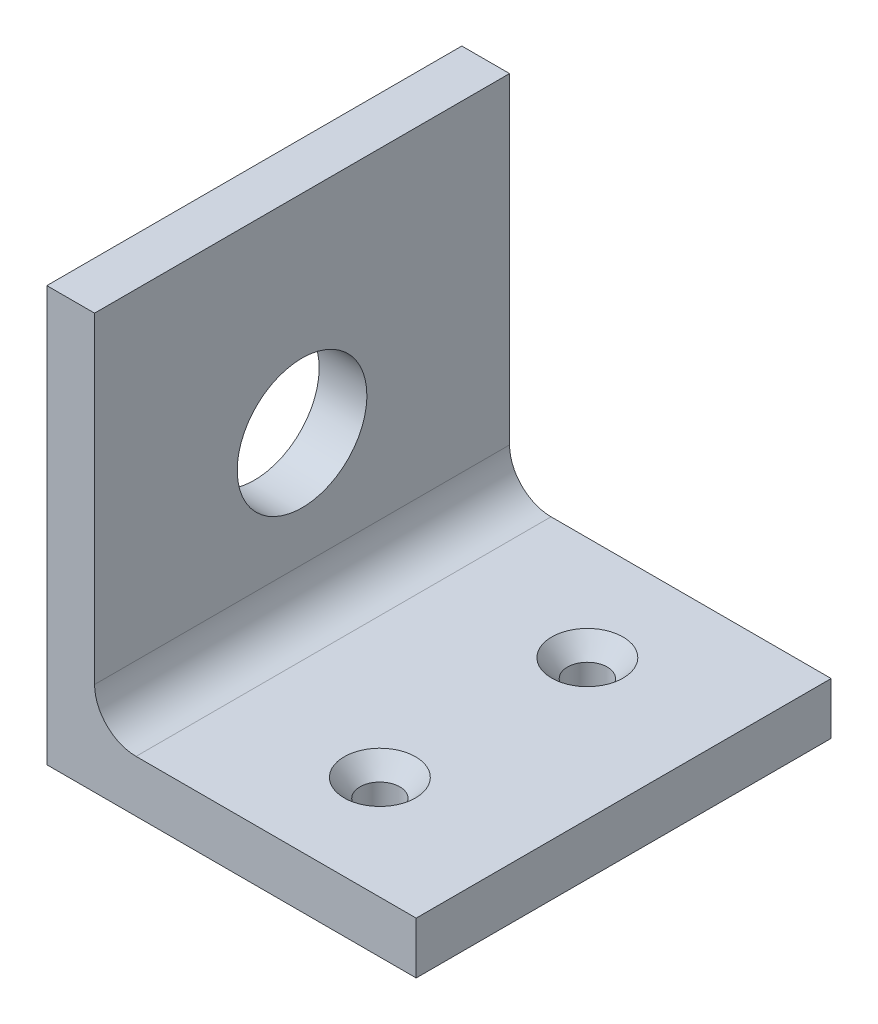
SolidWorks part; units mm, degrees
material "6061-T6 (SS)"
ref_plane "Front Plane" through (0, 0, 0) normal (0, 0, 1) x (1, 0, 0)
ref_plane "Top Plane" through (0, 0, 0) normal (0, 1, 0) x (1, 0, 0)
ref_plane "Right Plane" through (0, 0, 0) normal (1, 0, 0) x (0, 0, -1)
sketch "Sketch1" plane through (0, 0, 0) normal (0, 0, 1) x (1, 0, 0)
  line L0 (0, 0) -> (25.4, 0)
  line L1 (25.4, 0) -> (25.4, 3.175)
  line L2 (25.4, 3.175) -> (3.175, 3.175)
  line L3 (3.175, 3.175) -> (3.175, 25.4)
  line L4 (3.175, 25.4) -> (0, 25.4)
  line L5 (0, 25.4) -> (0, 0)
  dimension "D1" = 3.175
  dimension "D2" = 25.4
extrude "Boss-Extrude1" add sketch "Sketch1" along normal blind 25.4
sketch "Sketch5" plane through (3.175, 0, 0) normal (1, 0, 0) x (0, 0, -1)
  line L0 (-25.4, 25.4) -> (0, 25.4) construction
  line L1 (0, 3.175) -> (0, 25.4) construction
  circle A0 centre (-12.7, 12.7) radius 3.9688
  dimension "D1" = 12.7
  dimension "D2" = 12.7
  dimension "D3" = 7.9375
extrude "Cut-Extrude2" cut sketch "Sketch5" against normal through all
sketch "Sketch6" plane through (0, 3.175, 0) normal (0, 1, 0) x (1, 0, 0)
  line L0 (14.2875, 0) -> (14.2875, -25.4) construction
  line L1 (25.4, 0) -> (3.175, 0) construction
  line L2 (25.4, -25.4) -> (3.175, -25.4) construction
  line L3 (0, -25.4) -> (25.4, -25.4) construction
  circle A0 centre (14.2875, -19.05) radius 1.5875 construction
  circle A1 centre (14.2875, -6.35) radius 1.5875 construction
  dimension "D1" = 6.35
  dimension "D2" = 12.7
  dimension "D3" = 3.175
hole_wizard "CSK for #2 Flat Head Machine Screw1" positions "Sketch7" profile "Sketch8" countersink size "#2" standard "ANSI Inch" end condition up to next
sketch "Sketch7" plane through (0, 3.175, 0) normal (0, 1, 0) x (1, 0, 0)
  point P0 (14.2875, -19.05)
  point P3 (14.2875, -6.35)
sketch "Sketch8" plane through (14.2875, 3.175, 19.05) normal (1, 0, 0) x (0, 0, 1)
  line L0 (0, 0) -> (0, 3.175)
  line L1 (0, 3.175) -> (1.2192, 3.175)
  line L2 (1.2192, 3.175) -> (1.2192, 1.1103)
  line L3 (1.2192, 1.1103) -> (2.1844, 0)
  line L5 (2.1844, 0) -> (0, 0)
  line L6 (-1.2192, 1.1103) -> (-2.1844, 0) construction
  line L11 (0, -6.35) -> (0, 107.95) construction
  dimension "Thru Hole Dia." = 2.4384
  dimension "Thru Hole Depth" = 3.175
  dimension "Near C'Sink Dia." = 4.3688
  dimension "Near C'Sink Angle" = 82
sketch "Sketch2" plane through (0, 0, 25.4) normal (0, 0, 1) x (1, 0, 0)
  line L0 (3.175, 3.175) -> (0, 0) construction
ref_plane "Plane1" through (0, 0, 0) normal (0.7071, -0.7071, 0) x (-0.7071, -0.7071, 0)
sketch "Sketch4" plane through (0, 3.175, 0) normal (0, 1, 0) x (1, 0, 0)
  line L0 (25.4, -12.7) -> (0, -12.7) construction
  line L1 (25.4, -25.4) -> (25.4, 0) construction
  circle A0 centre (12.7, -12.7) radius 1.5875
  dimension "D1" = 3.175
  dimension "D2" = 25.4
extrude "Cut-Extrude1" [suppressed] cut sketch "Sketch4" against normal through all
mirror "Mirror1" [suppressed] about plane through (0, 0, 0) normal (0.7071, -0.7071, 0)
sketch "Sketch9" plane through (0, 3.175, 0) normal (0, 1, 0) x (1, 0, 0)
  line L0 (25.4, 0) -> (3.175, 0) construction
  line L1 (25.4, -25.4) -> (22.86, -25.4)
  line L2 (25.4, -25.4) -> (25.4, 0)
  line L3 (25.4, 0) -> (22.86, 0)
  line L4 (22.86, -25.4) -> (22.86, 0)
  dimension "D1" = 2.54
extrude "Cut-Extrude3" cut sketch "Sketch9" against normal through all
fillet "Fillet1" radius 2.54 1 edges at (3.175, 3.175, 12.7)
fillet "Fillet2" [suppressed] radius 2.54
sketch "Sketch10" plane through (0, 25.4, 0) normal (0, 1, 0) x (1, 0, 0)
  line L0 (3.175, -25.4) -> (0, -25.4) construction
  line L1 (0, 0) -> (0.254, 0)
  line L2 (0, 0) -> (0, -25.4)
  line L3 (0, -25.4) -> (0.254, -25.4)
  line L4 (0.254, 0) -> (0.254, -25.4)
  dimension "D1" = 0.254
extrude "Cut-Extrude4" cut sketch "Sketch10" against normal through all
sketch "Sketch11" [suppressed] plane through (0, 0, 25.4) normal (0, 0, 1) x (1, 0, 0)
  line L0 (0, 50.8) -> (0, 0) construction
  line L1 (0, 25.4) -> (0.254, 25.4)
  line L2 (0, 25.4) -> (0, 0)
  line L3 (0, 0) -> (0.254, 0)
  line L4 (0.254, 25.4) -> (0.254, 0)
  line L5 (0, 0) -> (25.4, 0) construction
  dimension "D1" = 0.254
extrude "Cut-Extrude5" [suppressed] cut sketch "Sketch11" against normal through all
sketch "Sketch12" [suppressed] plane through (0, 0, 25.4) normal (0, 0, 1) x (1, 0, 0)
  line L0 (3.175, 5.715) -> (3.175, 25.4) construction
  line L1 (0.254, 25.4) -> (3.175, 25.4)
  line L2 (0.254, 25.4) -> (0.254, 25.146)
  line L3 (0.254, 25.146) -> (3.175, 25.146)
  line L4 (3.175, 25.4) -> (3.175, 25.146)
  dimension "D1" = 0.254
extrude "Cut-Extrude6" [suppressed] cut sketch "Sketch12" against normal through all
equation "\"Thick\"= \"in\""
